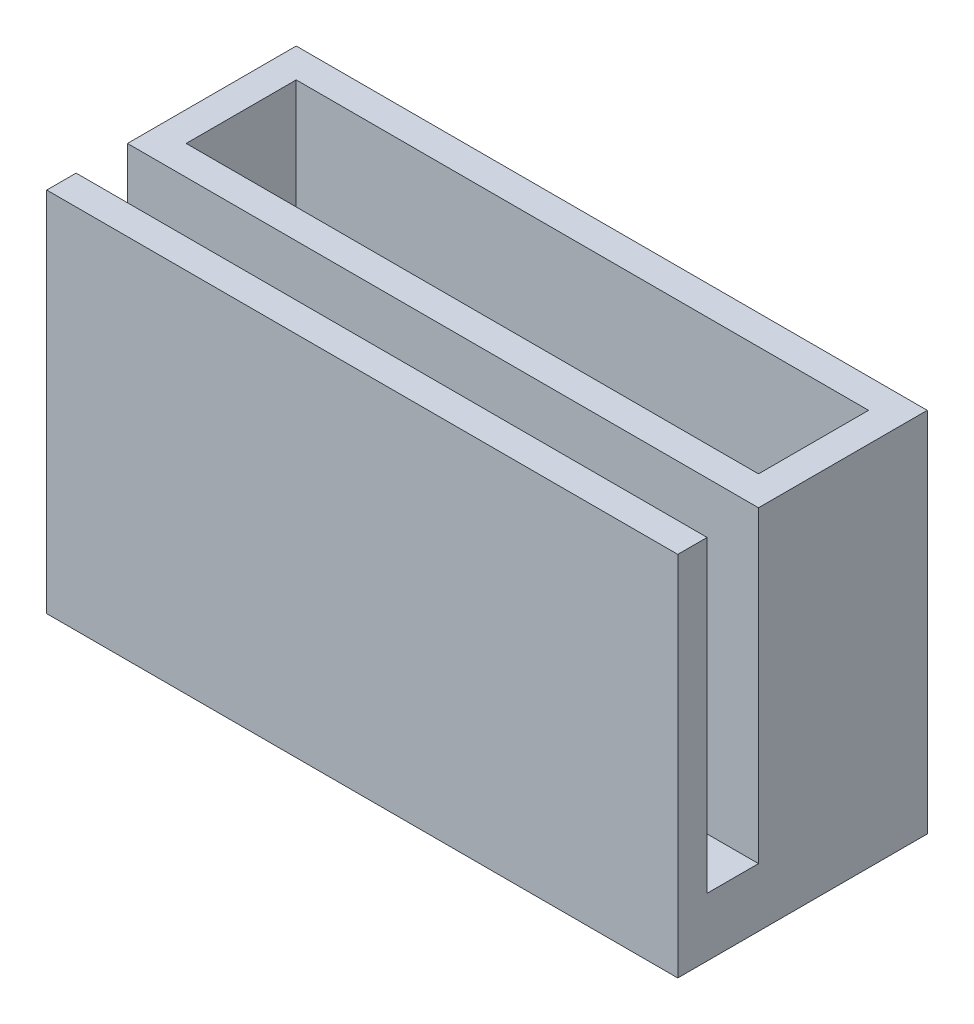
SolidWorks part; units mm, degrees
ref_plane "Front Plane" through (0, 0, 0) normal (0, 0, 1) x (1, 0, 0)
ref_plane "Top Plane" through (0, 0, 0) normal (0, 1, 0) x (1, 0, 0)
ref_plane "Right Plane" through (0, 0, 0) normal (1, 0, 0) x (0, 0, -1)
sketch "Sketch1" plane through (0, 0, 0) normal (0, 1, 0) x (1, 0, 0)
  line L0 (-2, -2) -> (41, -2)
  line L1 (0, 0) -> (39, 0)
  line L2 (0, 0) -> (0, 7.5)
  line L3 (0, 7.5) -> (39, 7.5)
  line L4 (39, 0) -> (39, 7.5)
  line L5 (0, 0) -> (39, 7.5) construction
  line L6 (0, 7.5) -> (39, 0) construction
  line L7 (41, -2) -> (41, 9.5)
  line L8 (-2, 9.5) -> (41, 9.5)
  line L9 (-2, -2) -> (-2, 9.5)
  point P4 (19.5, 3.75)
  dimension "D1" = 7.5
  dimension "D2" = 39
  dimension "D3" = 2
extrude "Boss-Extrude1" add sketch "Sketch1" along normal blind 25
sketch "Sketch2" plane through (0, 0, 0) normal (0, -1, 0) x (1, 0, 0)
  line L0 (41, 2) -> (41, -9.5) construction
  line L1 (-2, 2) -> (41, 2)
  line L2 (-2, 2) -> (-2, 7.5)
  line L3 (-2, 7.5) -> (41, 7.5)
  line L4 (41, 2) -> (41, 7.5)
  line L5 (-2, 2) -> (41, 7.5) construction
  line L6 (-2, 7.5) -> (41, 2) construction
  point P4 (19.5, 4.75)
  dimension "D1" = 5.5
extrude "Boss-Extrude2" add sketch "Sketch2" against normal blind 4
sketch "Sketch3" plane through (0, 4, 0) normal (0, 1, 0) x (1, 0, 0)
  line L0 (-2, -7.5) -> (-2, -2) construction
  line L1 (41, -7.5) -> (-2, -7.5)
  line L2 (41, -7.5) -> (41, -5.5)
  line L3 (41, -5.5) -> (-2, -5.5)
  line L4 (-2, -7.5) -> (-2, -5.5)
  line L5 (41, -7.5) -> (-2, -5.5) construction
  line L6 (41, -5.5) -> (-2, -7.5) construction
  point P4 (19.5, -6.5)
  dimension "D1" = 2
extrude "Boss-Extrude3" add sketch "Sketch3" along normal up to surface (21 mm away) up to face at (19.5, 25, -3.75)
